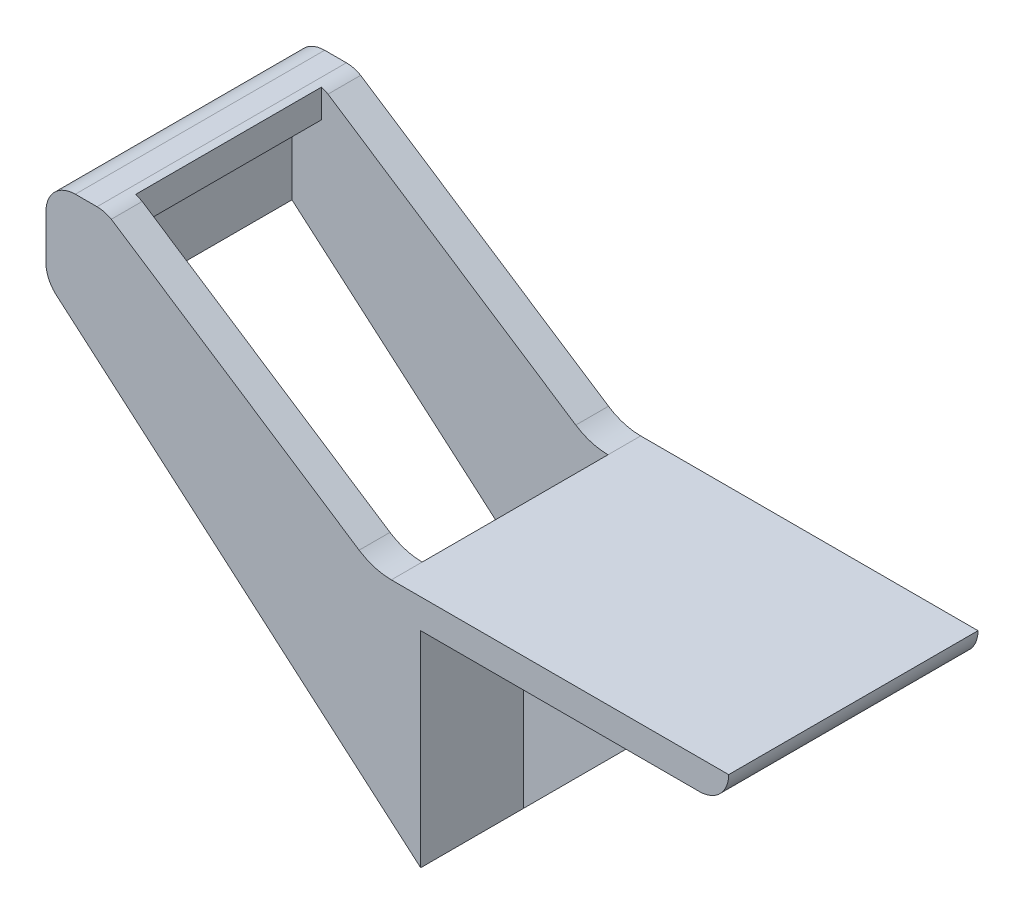
SolidWorks part; units mm, degrees
ref_plane "Front Plane" through (0, 0, 0) normal (0, 0, 1) x (1, 0, 0)
ref_plane "Top Plane" through (0, 0, 0) normal (0, 1, 0) x (1, 0, 0)
ref_plane "Right Plane" through (0, 0, 0) normal (1, 0, 0) x (0, 0, -1)
sketch "Sketch1" plane through (0, 0, 0) normal (0, 0, 1) x (1, 0, 0)
  line L0 (66.675, 0) -> (-6.35, 0)
  line L1 (66.675, 0) -> (60.325, 0) construction
  line L2 (60.325, -6.35) -> (0, -6.35)
  line L3 (0, -6.35) -> (0, -50.8)
  line L4 (-66.971, 37.2977) -> (-13.3187, 2.0827)
  line L5 (-70.0607, 38.1) -> (-74.7617, 38.1)
  line L6 (-81.1117, 31.75) -> (-81.1117, 21.9617)
  line L7 (-78.9053, 17.15) -> (0, -50.8)
  arc A0 (60.325, -6.35) -> (66.675, 0) centre (60.325, 0) ccw
  arc A1 (-13.3187, 2.0827) -> (-6.35, 0) centre (-6.35, 12.7) ccw
  arc A2 (-81.1117, 31.75) -> (-74.7617, 38.1) centre (-74.7617, 31.75) cw
  arc A3 (-81.1117, 21.9617) -> (-78.9053, 17.15) centre (-74.7617, 21.9617) ccw
  arc A4 (-70.0607, 38.1) -> (-66.971, 37.2977) centre (-70.0607, 31.75) cw
  point P11 (0, 0)
  point P15 (-81.1117, 38.1)
  point P18 (-81.1117, 19.05)
  point P21 (-68.4117, 38.1)
  dimension "D4" = 12.7
  dimension "D6" = 60.325
  dimension "D8" = 6.35
  dimension "D9" = 6.35
  dimension "D3" = 12.7
  dimension "D1" = 73.025
  dimension "D2" = 6.35
  dimension "D5" = 88.9
  dimension "D7" = 19.05
  dimension "D10" = 17.15
  dimension "D11" = 50.8
  dimension "D12" = 12.7
  dimension "D13" = 70.0607
  dimension "D14" = 64.1768
extrude "Boss-Extrude2" add sketch "Sketch1" along normal mid plane 53.975 contours L4 A1 L0 A0 L2 L3 L7 A3 L6 A2 L5 A4
sketch "Sketch3" plane through (0, 0, 0) normal (0, 1, 0) x (1, 0, 0)
  line L0 (-81.1117, -26.9875) -> (-81.1117, 26.9875) construction
  line L1 (-6.35, 19.9171) -> (-68.4117, 19.9171)
  line L2 (-6.35, 19.9171) -> (-6.35, -20.3089)
  line L3 (-6.35, -20.3089) -> (-68.4117, -20.3089)
  line L4 (-68.4117, 19.9171) -> (-68.4117, -20.3089)
  line L5 (66.675, -26.9875) -> (66.675, 26.9875) construction
  dimension "D1" = 12.7
  dimension "D2" = 73.025
extrude "Cut-Extrude1" cut sketch "Sketch3" along normal through all and the other way through all
sketch "Sketch4" plane through (0, 0, 0) normal (0, 1, 0) x (1, 0, 0)
  line L0 (-81.1117, -26.9875) -> (-81.1117, 26.9875) construction
  line L1 (-68.4117, 19.9171) -> (-74.7617, 19.9171)
  line L2 (-68.4117, 19.9171) -> (-68.4117, -20.3089)
  line L3 (-68.4117, -20.3089) -> (-74.7617, -20.3089)
  line L4 (-74.7617, 19.9171) -> (-74.7617, -20.3089)
  dimension "D1" = 6.35
extrude "Cut-Extrude2" cut sketch "Sketch4" along normal offset from surface (31.75 mm away) 6.35 up to face at (-72.4112, 38.1, 0)
sketch "Sketch5" plane through (0, 0, 0) normal (0, 0, 1) x (1, 0, 0)
  line L0 (0, -50.8) -> (44.45, -6.35)
  line L1 (60.325, -6.35) -> (0, -6.35) construction
  line L2 (0, -6.35) -> (0, -50.8) construction
  line L3 (44.45, -6.35) -> (0, -6.35)
  line L4 (0, -6.35) -> (0, -50.8)
  dimension "D1" = 45
extrude "Boss-Extrude3" add sketch "Sketch5" along normal mid plane 9.525
